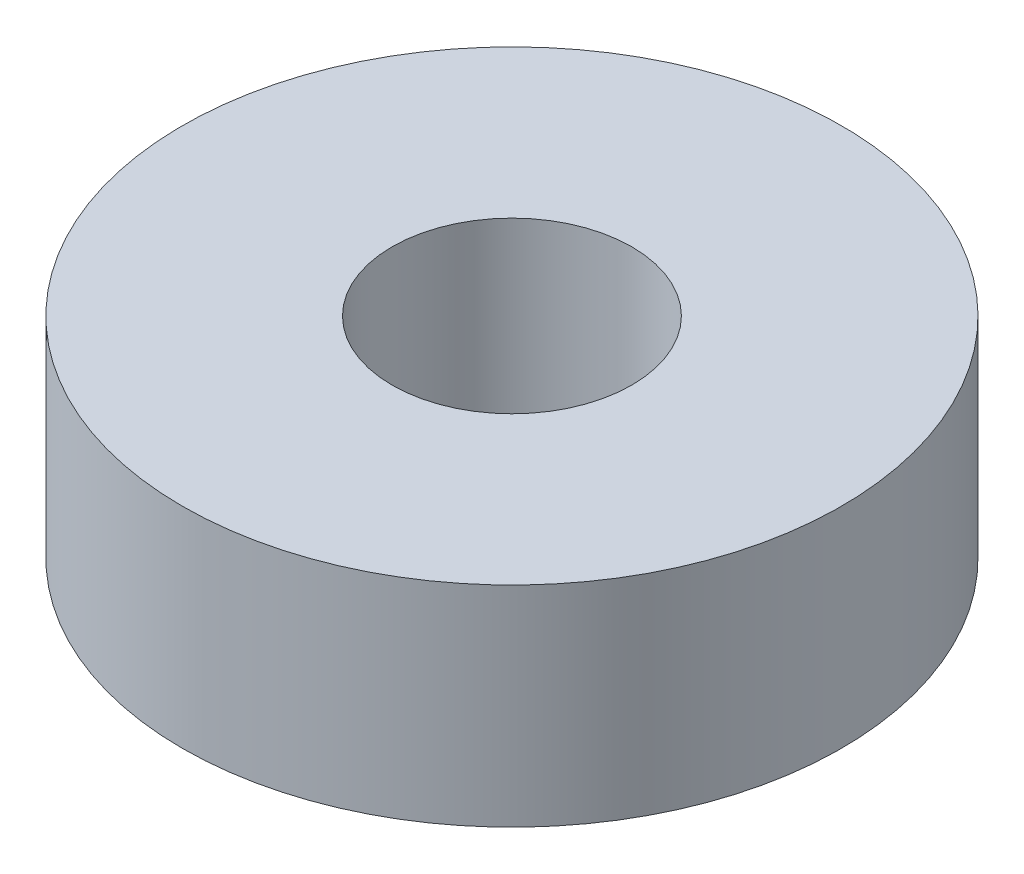
SolidWorks part; units mm, degrees
ref_plane "Front Plane" through (0, 0, 0) normal (0, 0, 1) x (1, 0, 0)
ref_plane "Top Plane" through (0, 0, 0) normal (0, 1, 0) x (1, 0, 0)
ref_plane "Right Plane" through (0, 0, 0) normal (1, 0, 0) x (0, 0, -1)
sketch "Sketch1" plane through (0, 0, 0) normal (0, 1, 0) x (1, 0, 0)
  circle A0 centre (0, 0) radius 11
  circle A1 centre (0, 0) radius 4
  dimension "D1" = 22
  dimension "D2" = 8
extrude "Boss-Extrude1" add sketch "Sketch1" along normal blind 7
